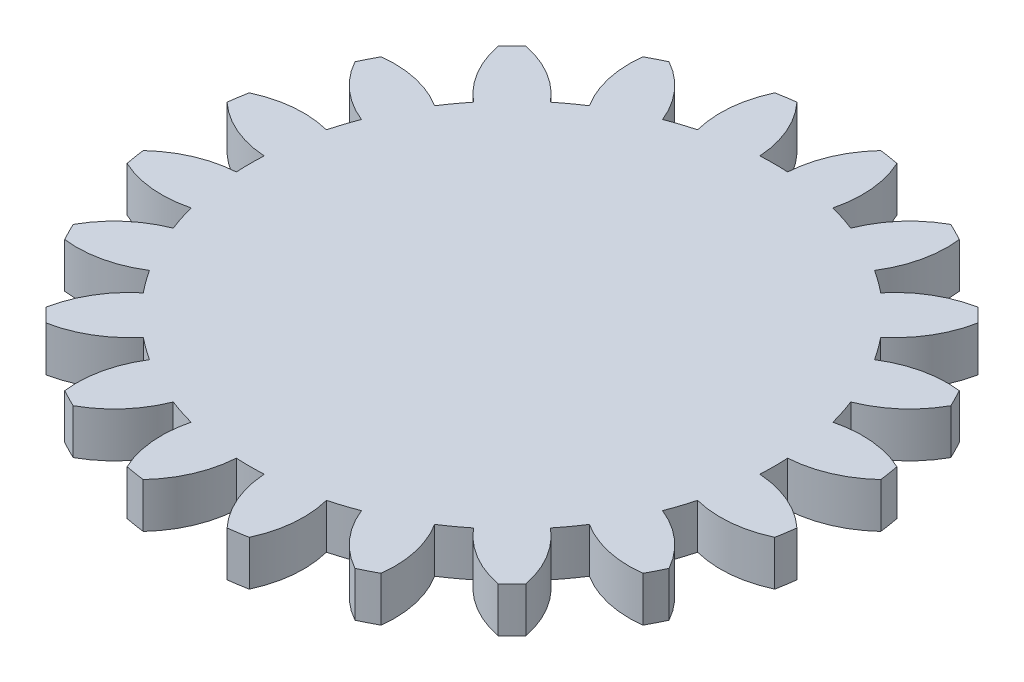
SolidWorks part; units mm, degrees
ref_plane "Alzado" through (0, 0, 0) normal (0, 0, 1) x (1, 0, 0)
ref_plane "Planta" through (0, 0, 0) normal (0, 1, 0) x (1, 0, 0)
ref_plane "Vista lateral" through (0, 0, 0) normal (1, 0, 0) x (0, 0, -1)
sketch "Croquis1" plane through (0, 0, 0) normal (0, 1, 0) x (1, 0, 0)
  circle A0 centre (0, 0) radius 22
  dimension "De" = 44
extrude "Saliente-Extruir1" add sketch "Croquis1" along normal blind 3
sketch "Croquis2" plane through (0, 3, 0) normal (0, 1, 0) x (1, 0, 0)
  line L0 (0, 0) -> (0, 68.4929) construction
  line L1 (1.5708, 20) -> (7.9333, 17.0374) construction
  circle A0 centre (0, 0) radius 20 construction
  circle A1 centre (0, 0) radius 17.5 construction
  circle A2 centre (0, 0) radius 18.7939 construction
  circle A3 centre (0, 20) radius 1.5708 construction
  arc A4 (0.9285, 17.4753) -> (2.7979, 21.8214) centre (7.9333, 17.0374) cw
  circle A5 centre (0, 0) radius 22 construction
  arc A7 (-0.9285, 17.4753) -> (-2.7979, 21.8214) centre (-7.9333, 17.0374) ccw
  arc A8 (-0.9285, 17.4753) -> (0.9285, 17.4753) centre (0, 0) cw
  arc A9 (2.7979, 21.8214) -> (-2.7979, 21.8214) centre (0, 0) ccw
  dimension "Dp" = 40
  dimension "Df" = 35
  dimension "Ct" = 37.5877
  dimension "C" = 3.1416
extrude "Cortar-Extruir1" cut sketch "Croquis2" against normal up to surface (3 mm away) up to face at (0, 0, 22)
pattern_circular "MatrizC1" count 20 over 360 about axis through (0, 0, 0) along (0, 1, 0) of "Cortar-Extruir1"
